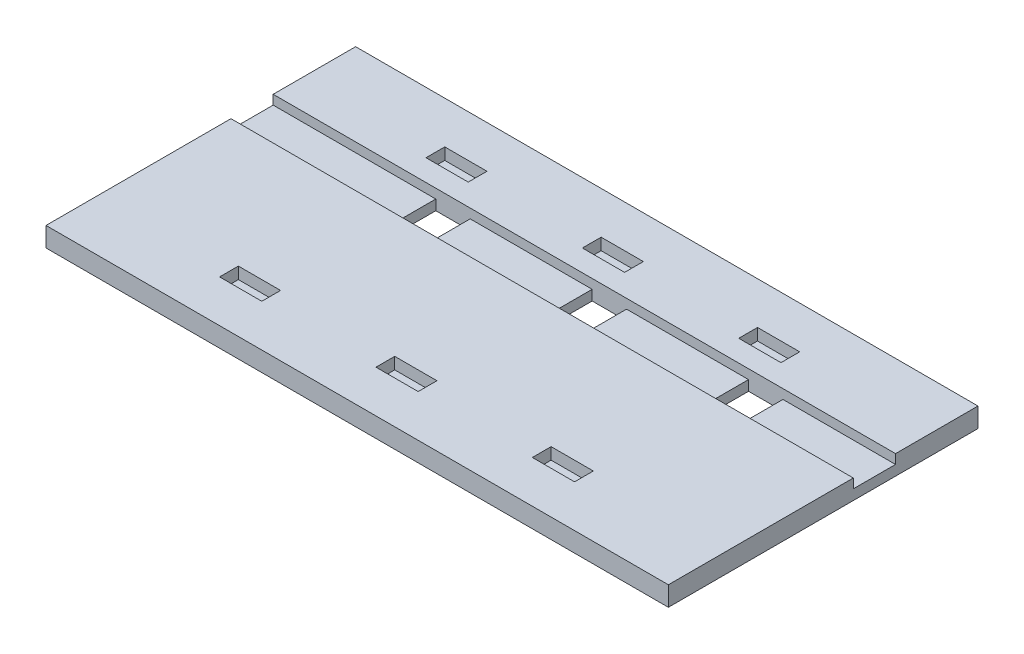
SolidWorks part; units mm, degrees
material "POLYURETHANE (11671)"
ref_plane "Front Plane" through (0, 0, 0) normal (0, 0, 1) x (1, 0, 0)
ref_plane "Top Plane" through (0, 0, 0) normal (0, 1, 0) x (1, 0, 0)
ref_plane "Right Plane" through (0, 0, 0) normal (1, 0, 0) x (0, 0, -1)
sketch "Sketch1" plane through (0, 0, 0) normal (0, 1, 0) x (1, 0, 0)
  line L1 (-50.546, -25.146) -> (50.546, -25.146)
  line L2 (-50.546, -25.146) -> (-50.546, 25.146)
  line L3 (-50.546, 25.146) -> (50.546, 25.146)
  line L4 (50.546, -25.146) -> (50.546, 25.146)
  line L5 (0, 25.146) -> (0, -25.146) construction
  line L6 (-50.546, 0) -> (50.546, 0) construction
  point P0 (0, 0)
  dimension "D1" = 50.292
  dimension "D2" = 101.092
extrude "Boss-Extrude1" add sketch "Sketch1" along normal blind 3.175
sketch "Sketch2" plane through (0, 3.175, 0) normal (0, 1, 0) x (1, 0, 0)
  line L0 (1.27, 4.8935) -> (6.858, 4.8935)
  line L1 (1.27, 4.8935) -> (1.27, 11.7515)
  line L2 (6.858, 4.8935) -> (6.858, 11.7515)
  line L3 (1.27, 11.7515) -> (6.858, 11.7515)
  circle A0 centre (4.064, 0) radius 5.635 construction
  dimension "D1" = 11.27
  dimension "D2" = 4.064
  dimension "D3" = 5.588
  dimension "D4" = 6.858
extrude "Wire Hole" cut sketch "Sketch2" against normal through all contours L3 L1 L0 L2
sketch "Sketch3" plane through (0, 3.175, 0) normal (0, 1, 0) x (1, 0, 0)
  line L0 (-3.81, 15.24) -> (3.048, 15.24)
  line L1 (-3.81, 15.24) -> (-3.81, 18.288)
  line L2 (3.048, 15.24) -> (3.048, 18.288)
  line L3 (-3.81, 18.288) -> (3.048, 18.288)
  line L4 (-3.4925, 0) -> (3.4925, 0) construction
  dimension "D1" = 3.048
  dimension "D2" = 6.858
  dimension "D3" = 3.048
  dimension "D4" = 15.24
extrude "Cut-Extrude2" cut sketch "Sketch3" against normal blind 1.905
mirror "Mirror1" about plane through (0, 0, 0) normal (0, 0, 1) of "Cut-Extrude2"
pattern_linear "LPattern1" count 2 spacing 25.4 along (-1, 0, 0) count 2 spacing 25.4 along (1, 0, 0) of "Wire Hole", "Cut-Extrude2", "Mirror1"
sketch "Sketch4" plane through (0, 3.175, 0) normal (0, 1, 0) x (1, 0, 0)
  line L0 (-50.546, 25.146) -> (-50.546, -25.146) construction
  line L1 (-50.546, 11.7515) -> (50.546, 11.7515)
  line L2 (-50.546, 11.7515) -> (-50.546, 4.8935)
  line L3 (-50.546, 4.8935) -> (50.546, 4.8935)
  line L4 (50.546, 11.7515) -> (50.546, 4.8935)
  line L5 (50.546, -25.146) -> (50.546, 25.146) construction
  line L7 (1.27, 11.7515) -> (6.858, 11.7515) construction
  line L8 (1.27, 4.8935) -> (6.858, 4.8935) construction
extrude "Cut-Extrude3" cut sketch "Sketch4" against normal blind 1.524
equation "\"Arrow Height\"= 1in"
equation "\"Button Height\"= 2in"
equation "\"Button Width\"= 4in"
equation "\"Haptic Diameter\"= 10mm"
equation "\"Haptic Thickness\"= 2.7mm"
equation "\"D1@Sketch1\"=\"Button Height\"-\"Tolerance\""
equation "\"D2@Sketch1\"=\"Button Width\"-\"Tolerance\""
equation "\"Arrow Spacing\"= 1in"
equation "\"Arrow Width\"= 0.75in"
equation "\"Haptic Wire Angle\"= 63.43"
equation "\"Haptic Wire Width\"= .2in"
equation "\"Hatic Wire Height\"= .25in"
equation "\"D1@Sketch2\"=\"Haptic Diameter\"+.05"
equation "\"D3@Sketch2\"=\"Haptic Wire Width\"+.02"
equation "\"D4@Sketch2\"=\"Hatic Wire Height\"+.02"
equation "\"Tolerance\"= .02in"
